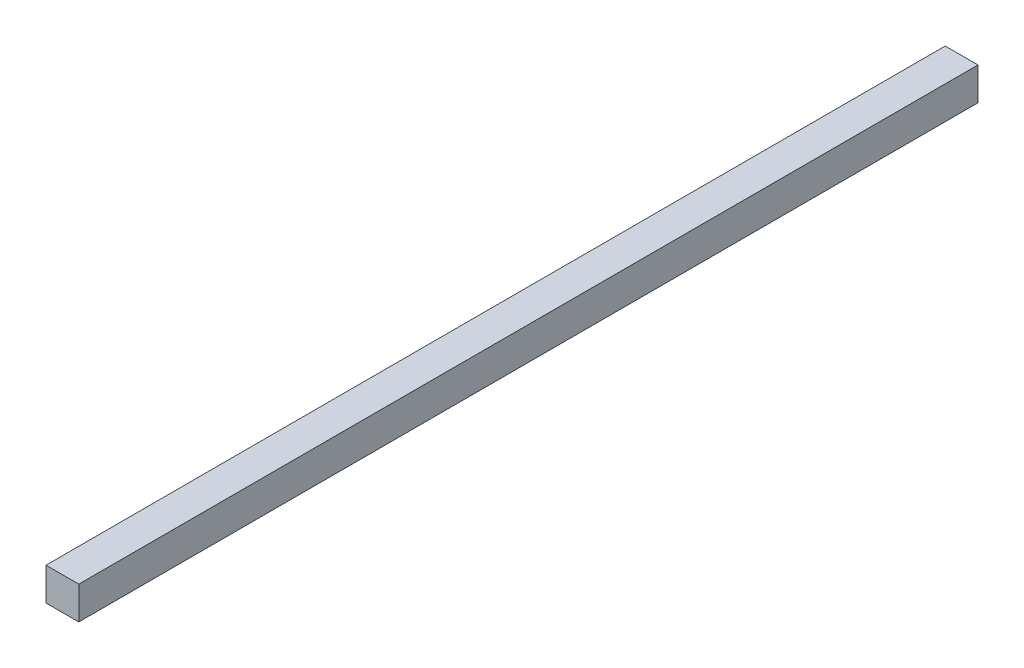
SolidWorks part; units mm, degrees
ref_plane "Front Plane" through (0, 0, 0) normal (0, 0, 1) x (1, 0, 0)
ref_plane "Top Plane" through (0, 0, 0) normal (0, 1, 0) x (1, 0, 0)
ref_plane "Right Plane" through (0, 0, 0) normal (1, 0, 0) x (0, 0, -1)
sketch "Sketch1" plane through (0, 0, 0) normal (0, 1, 0) x (1, 0, 0)
  line L1 (0, 0) -> (88.9, 0)
  line L2 (0, 0) -> (0, -2438.4)
  line L3 (0, -2438.4) -> (88.9, -2438.4)
  line L4 (88.9, 0) -> (88.9, -2438.4)
extrude "Boss-Extrude1" add sketch "Sketch1" along normal blind 88.9
sketch "Sketch2" plane through (0, 0, 0) normal (-1, 0, 0) x (0, 0, 1)
  line L0 (0, 44.45) -> (1219.2, 44.45)
  line L1 (0, 88.9) -> (0, 0) construction
  line L2 (1219.2, 44.45) -> (2438.4, 44.45)
  line L3 (2438.4, 88.9) -> (2438.4, 0) construction
  line L4 (1219.2, 88.9) -> (1219.2, 0)
  line L5 (0, 88.9) -> (2438.4, 88.9) construction
  line L6 (0, 0) -> (2438.4, 0) construction
